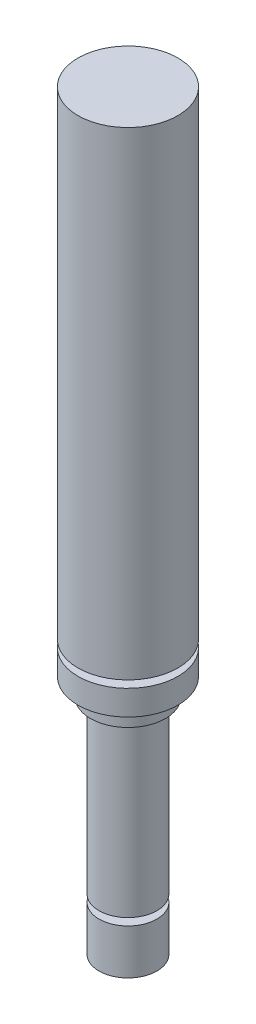
SolidWorks part; units mm, degrees
ref_plane "Front Plane" through (0, 0, 0) normal (0, 0, 1) x (1, 0, 0)
ref_plane "Top Plane" through (0, 0, 0) normal (0, 1, 0) x (1, 0, 0)
ref_plane "Right Plane" through (0, 0, 0) normal (1, 0, 0) x (0, 0, -1)
sketch "Sketch1" plane through (0, 0, 0) normal (0, 0, 1) x (1, 0, 0)
  line L0 (0, 8.4525) -> (0, -6.3086) construction
  line L1 (0, 0) -> (2, 0)
  line L3 (2, 15.4) -> (2.5875, 15.4)
  line L4 (2.5875, 15.4) -> (2.5875, 16.6321)
  line L5 (2.5875, 16.6321) -> (3.45, 16.6321)
  line L6 (3.45, 16.6321) -> (3.45, 18.3549)
  line L7 (3.45, 18.3549) -> (2.5875, 18.3549)
  line L8 (2.5875, 18.3549) -> (2.5875, 18.8549)
  line L9 (2.5875, 18.8549) -> (3.45, 18.8549)
  line L10 (3.45, 18.8549) -> (3.45, 51.9)
  line L11 (3.45, 51.9) -> (0, 51.9)
  line L12 (0, 51.9) -> (0, 0)
  line L13 (2, 0) -> (2, 3.1117)
  line L14 (2, 3.1117) -> (1.2993, 3.1117)
  line L15 (1.2993, 3.1117) -> (1.2993, 3.6117)
  line L16 (1.2993, 3.6117) -> (2, 3.6117)
  line L17 (2, 3.6117) -> (2, 15.4)
  point P16 (0, 0)
  point P20 (1, 0)
  point P21 (0, 0)
  dimension "D1" = 6.9
  dimension "D2" = 0.5
  dimension "D3" = 0.5
  dimension "D4" = 51.9
  dimension "D5" = 15.4
  dimension "D6" = 4
revolve "Revolve1" add sketch "Sketch1" angle 360 about L0
